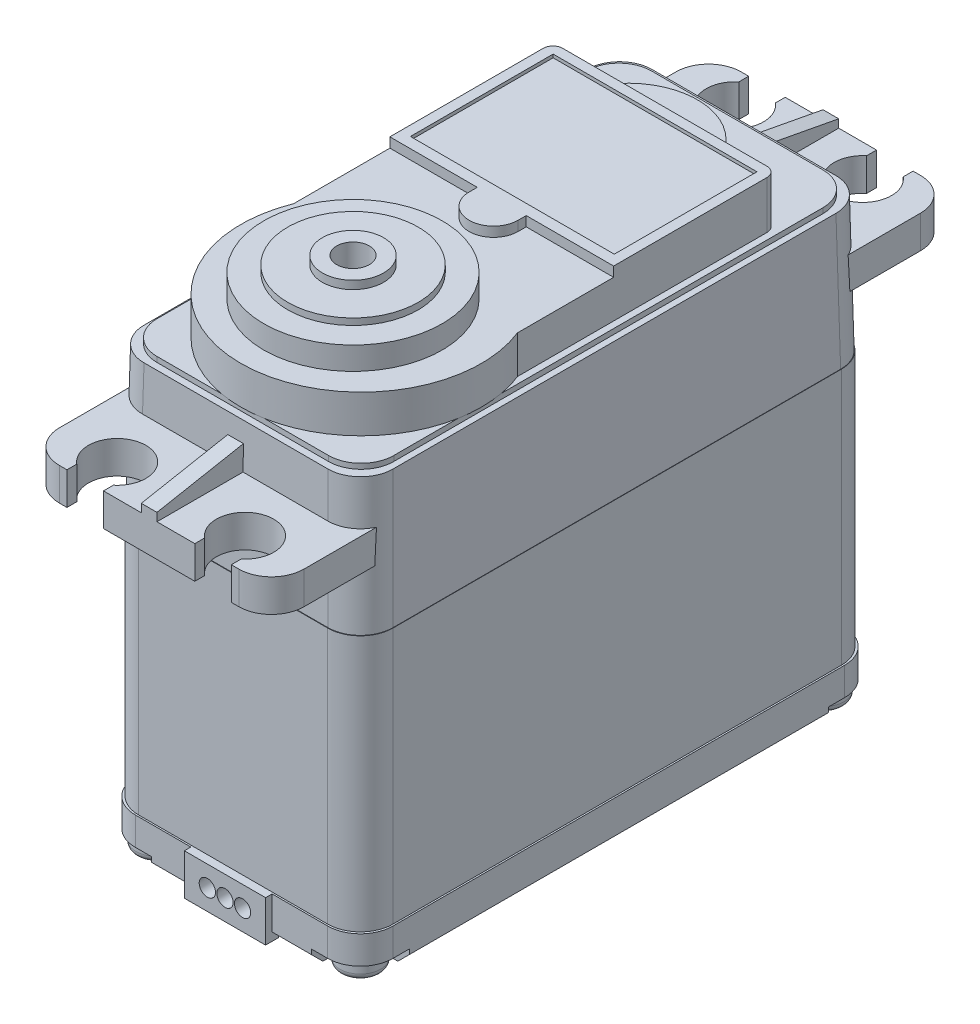
SolidWorks part; units mm, degrees
material "ABS"
ref_plane "Front Plane" through (0, 0, 0) normal (0, 0, 1) x (1, 0, 0)
ref_plane "Top Plane" through (0, 0, 0) normal (0, 1, 0) x (1, 0, 0)
ref_plane "Right Plane" through (0, 0, 0) normal (1, 0, 0) x (0, 0, -1)
sketch "Sketch1" plane through (0, 0, 0) normal (0, 1, 0) x (1, 0, 0)
  line L1 (-9.906, 20.0025) -> (9.906, 20.0025)
  line L2 (-9.906, 20.0025) -> (-9.906, -20.0025)
  line L3 (-9.906, -20.0025) -> (9.906, -20.0025)
  line L4 (9.906, 20.0025) -> (9.906, -20.0025)
  line L5 (-9.906, 20.0025) -> (9.906, -20.0025) construction
  line L6 (-9.906, -20.0025) -> (9.906, 20.0025) construction
  point P0 (0, 0)
  dimension "D1" = 19.812
  dimension "D2" = 40.005
extrude "Extrude1" add sketch "Sketch1" along normal blind 19.9644
sketch "Sketch2" plane through (0, 0, 0) normal (0, -1, 0) x (1, 0, 0)
  line L1 (-10.033, 20.1295) -> (10.033, 20.1295)
  line L2 (-10.033, 20.1295) -> (-10.033, -20.1295)
  line L3 (-10.033, -20.1295) -> (10.033, -20.1295)
  line L4 (10.033, 20.1295) -> (10.033, -20.1295)
  line L5 (-10.033, 20.1295) -> (10.033, -20.1295) construction
  line L6 (-10.033, -20.1295) -> (10.033, 20.1295) construction
  point P0 (0, 0)
  dimension "D1" = 40.259
  dimension "D2" = 20.066
extrude "Extrude2" add sketch "Sketch2" along normal blind 3.4544
sketch "Sketch3" plane through (0, 19.9644, 0) normal (0, 1, 0) x (1, 0, 0)
  line L1 (-9.8806, 19.9644) -> (9.8806, 19.9644)
  line L2 (-9.8806, 19.9644) -> (-9.8806, -19.9644)
  line L3 (-9.8806, -19.9644) -> (9.8806, -19.9644)
  line L4 (9.8806, 19.9644) -> (9.8806, -19.9644)
  line L5 (-9.8806, 19.9644) -> (9.8806, -19.9644) construction
  line L6 (-9.8806, -19.9644) -> (9.8806, 19.9644) construction
  point P0 (0, 0)
  dimension "D1" = 39.9288
  dimension "D2" = 19.7612
extrude "Extrude3" add sketch "Sketch3" along normal blind 10.5156 draft 1
sketch "Sketch4" plane through (0, 30.48, 0) normal (0, 1, 0) x (1, 0, 0)
  line L1 (-9.2202, 19.2532) -> (9.2202, 19.2532)
  line L2 (-9.2202, 19.2532) -> (-9.2202, -19.2532)
  line L3 (-9.2202, -19.2532) -> (9.2202, -19.2532)
  line L4 (9.2202, 19.2532) -> (9.2202, -19.2532)
  line L5 (-9.2202, 19.2532) -> (9.2202, -19.2532) construction
  line L6 (-9.2202, -19.2532) -> (9.2202, 19.2532) construction
  point P0 (0, 0)
  dimension "D1" = 18.4404
  dimension "D2" = 38.5064
extrude "Extrude4" add sketch "Sketch4" along normal blind 0.4064
fillet "Fillet1" radius 2.54 4 edges at (-9.2202, 30.6832, 19.2532) (9.2202, 30.6832, 19.2532) (9.2202, 30.6832, -19.2532) (-9.2202, 30.6832, -19.2532)
fillet "Fillet2" radius 2.54 4 edges at (-9.7888, 25.2222, 19.8726) (9.7888, 25.2222, 19.8726) (9.7888, 25.2222, -19.8726) (-9.7888, 25.2222, -19.8726)
fillet "Fillet3" radius 2.54 4 edges at (9.906, 9.9822, 20.0025) (-9.906, 9.9822, 20.0025) (-9.906, 9.9822, -20.0025) (9.906, 9.9822, -20.0025)
fillet "Fillet4" radius 2.54 4 edges at (10.033, -1.7272, -20.1295) (10.033, -1.7272, 20.1295) (-10.033, -1.7272, 20.1295) (-10.033, -1.7272, -20.1295)
sketch "Sketch5" plane through (0, -3.4544, 0) normal (0, -1, 0) x (1, 0, 0)
  line L0 (0, 20.1295) -> (0, -20.1295) construction
  line L1 (7.493, 20.1295) -> (-7.493, 20.1295) construction
  line L2 (-6.223, 20.1295) -> (6.223, 20.1295) construction
  line L3 (-6.223, -20.1295) -> (6.223, -20.1295) construction
  line L4 (10.033, 0) -> (-10.033, 0) construction
  line L5 (-10.033, 17.5895) -> (-10.033, -17.5895) construction
  line L6 (-10.033, 16.3195) -> (-10.033, -16.3195) construction
  line L7 (10.033, 16.3195) -> (10.033, -16.3195) construction
  line L8 (-6.223, 20.1295) -> (-6.223, 16.3195)
  line L9 (6.223, 20.1295) -> (6.223, 16.3195)
  line L10 (-10.033, 16.3195) -> (-6.223, 16.3195)
  line L11 (10.033, 16.3195) -> (6.223, 16.3195)
  line L12 (-10.033, -16.3195) -> (-6.223, -16.3195)
  line L13 (-6.223, -20.1295) -> (-6.223, -16.3195)
  line L14 (6.223, -20.1295) -> (6.223, -16.3195)
  line L15 (10.033, -16.3195) -> (6.223, -16.3195)
  line L16 (-7.493, 20.1295) -> (-6.223, 20.1295)
  line L17 (-10.033, 17.5895) -> (-10.033, 16.3195)
  line L18 (6.223, 20.1295) -> (7.493, 20.1295)
  line L19 (10.033, 17.5895) -> (10.033, 16.3195)
  line L20 (-10.033, -17.5895) -> (-10.033, -16.3195)
  line L21 (-7.493, -20.1295) -> (-6.223, -20.1295)
  line L22 (6.223, -20.1295) -> (7.493, -20.1295)
  line L23 (10.033, -16.3195) -> (10.033, -17.5895)
  arc A0 (-10.033, -17.5895) -> (-7.493, -20.1295) centre (-7.493, -17.5895) ccw construction
  arc A1 (-7.493, 20.1295) -> (-10.033, 17.5895) centre (-7.493, 17.5895) ccw construction
  arc A2 (10.033, 17.5895) -> (7.493, 20.1295) centre (7.493, 17.5895) ccw construction
  arc A3 (7.493, -20.1295) -> (10.033, -17.5895) centre (7.493, -17.5895) ccw construction
  arc A4 (-10.033, -17.5895) -> (-7.493, -20.1295) centre (-7.493, -17.5895) ccw
  arc A5 (7.493, -20.1295) -> (10.033, -17.5895) centre (7.493, -17.5895) ccw
  arc A6 (10.033, 17.5895) -> (7.493, 20.1295) centre (7.493, 17.5895) ccw
  arc A7 (-7.493, 20.1295) -> (-10.033, 17.5895) centre (-7.493, 17.5895) ccw
  dimension "D1" = 3.81
  dimension "D2" = 3.81
extrude "Extrude5" cut sketch "Sketch5" against normal blind 1.27
sketch "Sketch6" plane through (0, -2.1844, 0) normal (0, -1, 0) x (1, 0, 0)
  line L0 (0, 18.034) -> (0, -18.034) construction
  line L1 (-7.9375, 18.034) -> (7.9375, 18.034) construction
  line L2 (-7.9375, -18.034) -> (7.9375, -18.034) construction
  circle A0 centre (-7.9375, 18.034) radius 1.5875
  circle A1 centre (7.9375, 18.034) radius 1.5875
  circle A2 centre (7.9375, -18.034) radius 1.5875
  circle A3 centre (-7.9375, -18.034) radius 1.5875
  dimension "D3" = 3.175
  dimension "D1" = 15.875
  dimension "D2" = 36.068
extrude "Extrude7" add sketch "Sketch6" along normal blind 1.27
fillet "Fillet5" radius 0.508 4 edges at (7.9375, -3.4544, -19.6215) (-7.9375, -3.4544, -19.6215) (7.9375, -3.4544, 16.4465) (-7.9375, -3.4544, 16.4465)
sketch "Sketch7" plane through (0, -3.4544, 0) normal (0, -1, 0) x (1, 0, 0)
  line L0 (-9.525, 18.034) -> (-6.35, 18.034) construction
  line L1 (6.35, 18.034) -> (9.525, 18.034) construction
  line L2 (-9.525, -18.034) -> (-6.35, -18.034) construction
  line L3 (6.35, -18.034) -> (9.525, -18.034) construction
  line L5 (-8.1187, -16.9698) -> (-7.7563, -16.9698)
  line L6 (-8.1187, -16.9698) -> (-8.1187, -19.0982)
  line L7 (-8.1187, -19.0982) -> (-7.7563, -19.0982)
  line L8 (-7.7563, -16.9698) -> (-7.7563, -19.0982)
  line L9 (-8.1187, -16.9698) -> (-7.7563, -19.0982) construction
  line L10 (-8.1187, -19.0982) -> (-7.7563, -16.9698) construction
  line L11 (7.7563, -16.9698) -> (8.1187, -16.9698)
  line L12 (7.7563, -16.9698) -> (7.7563, -19.0982)
  line L13 (7.7563, -19.0982) -> (8.1187, -19.0982)
  line L14 (8.1187, -16.9698) -> (8.1187, -19.0982)
  line L15 (7.7563, -16.9698) -> (8.1187, -19.0982) construction
  line L16 (7.7563, -19.0982) -> (8.1187, -16.9698) construction
  line L17 (-8.1187, 19.0982) -> (-7.7563, 19.0982)
  line L18 (-8.1187, 19.0982) -> (-8.1187, 16.9698)
  line L19 (-8.1187, 16.9698) -> (-7.7563, 16.9698)
  line L20 (-7.7563, 19.0982) -> (-7.7563, 16.9698)
  line L21 (-8.1187, 19.0982) -> (-7.7563, 16.9698) construction
  line L22 (-8.1187, 16.9698) -> (-7.7563, 19.0982) construction
  line L23 (7.7563, 19.0982) -> (8.1187, 19.0982)
  line L24 (7.7563, 19.0982) -> (7.7563, 16.9698)
  line L25 (7.7563, 16.9698) -> (8.1187, 16.9698)
  line L26 (8.1187, 19.0982) -> (8.1187, 16.9698)
  line L27 (7.7563, 19.0982) -> (8.1187, 16.9698) construction
  line L28 (7.7563, 16.9698) -> (8.1187, 19.0982) construction
  circle A0 centre (-7.9375, 18.034) radius 1.5875 construction
  circle A1 centre (7.9375, 18.034) radius 1.5875 construction
  circle A2 centre (-7.9375, -18.034) radius 1.5875 construction
  circle A3 centre (-7.9375, -18.034) radius 1.5875 construction
  circle A4 centre (7.9375, -18.034) radius 1.5875 construction
  circle A5 centre (-7.9375, -18.034) radius 1.0795 construction
  circle A6 centre (7.9375, -18.034) radius 1.0795 construction
  circle A7 centre (-7.9375, 18.034) radius 1.0795 construction
  circle A8 centre (7.9375, 18.034) radius 1.0795 construction
  point P20 (-7.9375, -18.034)
  point P27 (7.9375, -18.034)
  point P34 (-7.9375, 18.034)
  point P41 (7.9375, 18.034)
extrude "Extrude8" cut sketch "Sketch7" against normal blind 0.508
sketch "Sketch8" plane through (0, -3.4544, 0) normal (0, -1, 0) x (1, 0, 0)
  line L0 (-7.9375, 19.6215) -> (-7.9375, 16.4465) construction
  line L1 (7.9375, 19.6215) -> (7.9375, 16.4465) construction
  line L2 (-7.9375, -16.4465) -> (-7.9375, -19.6215) construction
  line L3 (7.9375, -16.4465) -> (7.9375, -19.6215) construction
  line L4 (-7.7563, 19.0982) -> (-8.1187, 19.0982) construction
  line L5 (-9.0017, 18.2152) -> (-6.8733, 18.2152)
  line L6 (-9.0017, 18.2152) -> (-9.0017, 17.8528)
  line L7 (-9.0017, 17.8528) -> (-6.8733, 17.8528)
  line L8 (-6.8733, 18.2152) -> (-6.8733, 17.8528)
  line L9 (-9.0017, 18.2152) -> (-6.8733, 17.8528) construction
  line L10 (-9.0017, 17.8528) -> (-6.8733, 18.2152) construction
  line L12 (9.0017, 18.2152) -> (6.8733, 18.2152)
  line L13 (9.0017, 18.2152) -> (9.0017, 17.8528)
  line L14 (9.0017, 17.8528) -> (6.8733, 17.8528)
  line L15 (6.8733, 18.2152) -> (6.8733, 17.8528)
  line L16 (9.0017, 18.2152) -> (6.8733, 17.8528) construction
  line L17 (9.0017, 17.8528) -> (6.8733, 18.2152) construction
  line L18 (-9.0017, -17.8528) -> (-6.8733, -17.8528)
  line L19 (-9.0017, -17.8528) -> (-9.0017, -18.2152)
  line L20 (-9.0017, -18.2152) -> (-6.8733, -18.2152)
  line L21 (-6.8733, -17.8528) -> (-6.8733, -18.2152)
  line L22 (-9.0017, -17.8528) -> (-6.8733, -18.2152) construction
  line L23 (-9.0017, -18.2152) -> (-6.8733, -17.8528) construction
  line L24 (6.8733, -17.8528) -> (9.0017, -17.8528)
  line L25 (6.8733, -17.8528) -> (6.8733, -18.2152)
  line L26 (6.8733, -18.2152) -> (9.0017, -18.2152)
  line L27 (9.0017, -17.8528) -> (9.0017, -18.2152)
  line L28 (6.8733, -17.8528) -> (9.0017, -18.2152) construction
  line L29 (6.8733, -18.2152) -> (9.0017, -17.8528) construction
  circle A0 centre (-7.9375, 18.034) radius 1.5875 construction
  circle A1 centre (7.9375, 18.034) radius 1.5875 construction
  circle A2 centre (7.9375, 18.034) radius 1.5875 construction
  circle A3 centre (-7.9375, -18.034) radius 1.5875 construction
  circle A4 centre (7.9375, -18.034) radius 1.5875 construction
  arc A5 (-7.7563, 16.9698) -> (-7.7563, 19.0982) centre (-7.9375, 18.034) ccw construction
  arc A6 (7.7563, 19.0982) -> (7.7563, 16.9698) centre (7.9375, 18.034) ccw construction
  arc A7 (-7.7563, -19.0982) -> (-7.7563, -16.9698) centre (-7.9375, -18.034) ccw construction
  arc A8 (8.1187, -19.0982) -> (8.1187, -16.9698) centre (7.9375, -18.034) ccw construction
  point P21 (-7.9375, 18.034)
  point P31 (7.9375, 18.034)
  point P39 (-7.9375, -18.034)
  point P47 (7.9375, -18.034)
extrude "Extrude9" cut sketch "Sketch8" against normal blind 0.508
ref_plane "Plane1" through (0, 27.0256, 0) normal (0, -1, 0) x (1, 0, 0)
sketch "Sketch9" plane through (0, 27.0256, 0) normal (0, -1, 0) x (1, 0, 0)
  line L0 (0, -26.543) -> (0, 26.543) construction
  line L1 (-9.525, -26.543) -> (9.525, -26.543)
  line L2 (-9.525, 26.543) -> (9.525, 26.543)
  line L3 (-9.525, -26.543) -> (-9.525, 26.543)
  line L4 (9.525, -26.543) -> (9.525, 26.543)
  dimension "D1" = 53.086
  dimension "D2" = 19.05
extrude "Extrude10" add sketch "Sketch9" along normal blind 2.54
sketch "Sketch10" plane through (0, 27.0256, 0) normal (0, 1, 0) x (1, 0, 0)
  line L0 (0, 24.0538) -> (0, -24.0538) construction
  line L1 (4.9784, 24.0538) -> (-4.9784, 24.0538) construction
  line L2 (4.9784, -24.0538) -> (-4.9784, -24.0538) construction
  circle A0 centre (4.9784, 24.0538) radius 2.2352
  circle A1 centre (-4.9784, 24.0538) radius 2.2352
  circle A2 centre (4.9784, -24.0538) radius 2.2352
  circle A3 centre (-4.9784, -24.0538) radius 2.2352
  dimension "D3" = 4.4704
  dimension "D1" = 48.1076
  dimension "D2" = 9.9568
extrude "Extrude11" cut sketch "Sketch10" against normal through all
sketch "Sketch11" plane through (0, 27.0256, 0) normal (0, 1, 0) x (1, 0, 0)
  line L0 (-7.2136, 24.0538) -> (-2.7432, 24.0538) construction
  line L1 (2.7432, 24.0538) -> (7.2136, 24.0538) construction
  line L2 (-7.2136, -24.0538) -> (-2.7432, -24.0538) construction
  line L3 (2.7432, -24.0538) -> (7.2136, -24.0538) construction
  line L5 (-6.4008, 24.0538) -> (-3.556, 24.0538)
  line L6 (-6.4008, 24.0538) -> (-6.4008, 30.4038)
  line L7 (-6.4008, 30.4038) -> (-3.556, 30.4038)
  line L8 (-3.556, 24.0538) -> (-3.556, 30.4038)
  line L9 (3.556, 24.0538) -> (6.4008, 24.0538)
  line L10 (3.556, 24.0538) -> (3.556, 30.4038)
  line L11 (3.556, 30.4038) -> (6.4008, 30.4038)
  line L12 (6.4008, 24.0538) -> (6.4008, 30.4038)
  line L13 (-6.4008, -24.0538) -> (-3.556, -24.0538)
  line L14 (-6.4008, -24.0538) -> (-6.4008, -30.4038)
  line L15 (-6.4008, -30.4038) -> (-3.556, -30.4038)
  line L16 (-3.556, -24.0538) -> (-3.556, -30.4038)
  line L17 (3.556, -24.0538) -> (6.4008, -24.0538)
  line L18 (3.556, -24.0538) -> (3.556, -30.4038)
  line L19 (3.556, -30.4038) -> (6.4008, -30.4038)
  line L20 (6.4008, -24.0538) -> (6.4008, -30.4038)
  circle A0 centre (-4.9784, 24.0538) radius 2.2352 construction
  circle A1 centre (4.9784, 24.0538) radius 2.2352 construction
  circle A2 centre (-4.9784, -24.0538) radius 2.2352 construction
  circle A3 centre (4.9784, -24.0538) radius 2.2352 construction
  point P27 (-4.9784, 24.0538)
  point P28 (4.9784, 24.0538)
  point P29 (-4.9784, -24.0538)
  point P30 (4.9784, -24.0538)
  dimension "D1" = 2.8448
  dimension "D2" = 6.35
extrude "Extrude12" cut sketch "Sketch11" against normal through all
fillet "Fillet6" radius 2.54 4 edges at (9.525, 25.7556, 26.543) (-9.525, 25.7556, 26.543) (9.525, 25.7556, -26.543) (-9.525, 25.7556, -26.543)
sketch "Sketch12" plane through (0, -3.4544, 0) normal (0, -1, 0) x (1, 0, 0)
  circle A0 centre (0, 0) radius 0.9525
  dimension "D1" = 1.905
extrude "Extrude13" cut sketch "Sketch12" against normal blind 0.635
fillet "Fillet7" radius 0.254 1 edges at (0, -2.8194, -0.9525)
chamfer "Chamfer1" distance 0.889 angle 45 4 edges at (10.033, -3.4544, 0) (0, -3.4544, 20.1295) (0, -3.4544, -20.1295) (-10.033, -3.4544, 0)
sketch "Sketch13" plane through (0, 30.8864, 0) normal (0, 1, 0) x (1, 0, 0)
  line L0 (0, -19.7808) -> (0, -19.4056) construction
  line L1 (-6.6802, -19.2532) -> (6.6802, -19.2532) construction
  line L2 (-8.7122, 13.6144) -> (-4.572, 13.6144)
  line L3 (-7.1574, -19.7808) -> (7.1574, -19.7808) construction
  line L4 (0, -19.4056) -> (0, -19.2532) construction
  line L5 (0, -19.2532) -> (0, 13.6144) construction
  line L6 (-8.7122, 13.6144) -> (-8.7122, -6.5771)
  line L7 (8.7122, 13.6144) -> (8.7122, -6.5771)
  line L8 (0, 13.6144) -> (0, 16.1544) construction
  line L9 (-4.572, 13.6144) -> (4.572, 13.6144) construction
  line L10 (4.572, 13.6144) -> (8.7122, 13.6144)
  arc A0 (-8.7122, -6.5771) -> (8.7122, -6.5771) centre (0, -10.033) ccw
  arc A1 (-4.572, 13.6144) -> (4.572, 13.6144) centre (0, 10.7696) cw
  dimension "D1" = 18.7452
  dimension "D2" = 0.1524
  dimension "D3" = 17.4244
  dimension "D4" = 33.02
  dimension "D5" = 9.144
  dimension "D6" = 4.572
  dimension "D7" = 2.54
extrude "Extrude14" add sketch "Sketch13" along normal blind 2.9464
sketch "Sketch14" plane through (0, 33.8328, 0) normal (0, 1, 0) x (1, 0, 0)
  line L0 (8.7122, -6.5771) -> (8.7122, 13.6144) construction
  line L1 (-8.7122, 13.6144) -> (8.7122, 13.6144)
  line L2 (-8.7122, 13.6144) -> (-8.7122, 0.9144)
  line L3 (-8.7122, 0.9144) -> (-1.905, 0.9144)
  line L4 (8.7122, 13.6144) -> (8.7122, 0.9144)
  line L5 (0, 0.9144) -> (0, 13.6144) construction
  line L6 (0, 0.9144) -> (0, 0.2794) construction
  line L7 (0, 0.2794) -> (0, -1.6256) construction
  line L8 (-1.905, 0.2794) -> (-1.905, 0.9144)
  line L9 (1.905, 0.2794) -> (1.905, 0.9144)
  line L10 (1.905, 0.9144) -> (8.7122, 0.9144)
  arc A0 (-1.905, 0.2794) -> (1.905, 0.2794) centre (0, 0.2794) ccw
  dimension "D2" = 0.635
  dimension "D3" = 3.81
  dimension "D1" = 12.7
extrude "Extrude15" add sketch "Sketch14" along normal blind 0.762
sketch "Sketch15" plane through (0, 34.5948, 0) normal (0, 1, 0) x (1, 0, 0)
  line L0 (0, 13.6144) -> (0, 12.8524) construction
  line L1 (-7.9375, 12.8524) -> (7.9375, 12.8524)
  line L2 (-7.9375, 12.8524) -> (-7.9375, 1.7399)
  line L3 (-7.9375, 1.7399) -> (7.9375, 1.7399)
  line L4 (7.9375, 12.8524) -> (7.9375, 1.7399)
  line L5 (8.7122, 13.6144) -> (-8.7122, 13.6144) construction
  dimension "D1" = 15.875
  dimension "D2" = 11.1125
  dimension "D3" = 0.762
extrude "Extrude16" cut sketch "Sketch15" against normal blind 0.254
fillet "Fillet8" radius 0.762 2 edges at (-8.7122, 32.7406, -13.6144) (8.7122, 32.7406, -13.6144)
sketch "Sketch16" plane through (0, 33.8328, 0) normal (0, 1, 0) x (1, 0, 0)
  line L0 (0, -26.543) -> (0, -10.668) construction
  line L1 (3.556, -26.543) -> (-3.556, -26.543) construction
  circle A0 centre (0, -10.668) radius 6.9469
  dimension "D2" = 13.8938
  dimension "D1" = 15.875
extrude "Extrude17" add sketch "Sketch16" along normal blind 1.778
sketch "Sketch17" plane through (0, 35.6108, 0) normal (0, 1, 0) x (1, 0, 0)
  circle A0 centre (0, -10.668) radius 5.08
  dimension "D1" = 10.16
extrude "Extrude18" add sketch "Sketch17" along normal blind 0.508
sketch "Sketch18" plane through (0, 36.1188, 0) normal (0, 1, 0) x (1, 0, 0)
  circle A0 centre (0, -10.668) radius 2.3813
  dimension "D1" = 4.7625
extrude "Extrude19" add sketch "Sketch18" along normal blind 0.635
sketch "Sketch19" plane through (0, 36.7538, 0) normal (0, 1, 0) x (1, 0, 0)
  circle A0 centre (0, -10.668) radius 1.27
  dimension "D1" = 2.54
extrude "Extrude20" cut sketch "Sketch19" against normal blind 3.175
sketch "Sketch20" plane through (0, 0, 20.1295) normal (0, 0, 1) x (1, 0, 0)
  line L1 (-3.1623, 0) -> (3.1623, 0)
  line L2 (-3.1623, 0) -> (-3.1623, -3.2004)
  line L3 (-3.1623, -3.2004) -> (3.1623, -3.2004)
  line L4 (3.1623, 0) -> (3.1623, -3.2004)
  dimension "D1" = 6.3246
  dimension "D2" = 3.2004
extrude "Extrude21" add sketch "Sketch20" along normal blind 0.508 and the other way blind 0.508
sketch "Sketch21" plane through (0, 0, 20.6375) normal (0, 0, 1) x (1, 0, 0)
  line L0 (0, 0) -> (0, -3.2004) construction
  line L1 (-3.1623, -3.2004) -> (3.1623, -3.2004) construction
  line L2 (0, -1.6002) -> (1.3716, -1.6002) construction
  line L3 (0, -1.6002) -> (-1.3716, -1.6002) construction
  circle A0 centre (0, -1.6002) radius 0.635
  circle A1 centre (1.3716, -1.6002) radius 0.635
  circle A2 centre (-1.3716, -1.6002) radius 0.635
  dimension "D1" = 1.27
  dimension "D2" = 2.7432
extrude "Extrude22" cut sketch "Sketch21" against normal blind 2.54
sketch "Sketch22" plane through (0, 0, 0) normal (1, 0, 0) x (0, 0, -1)
  line L0 (-19.8079, 28.9306) -> (-26.543, 27.6606)
  line L1 (-19.8411, 27.0256) -> (-19.7808, 30.48) construction
  line L2 (-26.543, 27.6606) -> (-26.543, 27.0256)
  line L3 (-26.543, 27.0256) -> (-19.8411, 27.0256)
  line L4 (-19.8411, 27.0256) -> (-19.8079, 28.9306)
  line L5 (19.8411, 27.0256) -> (26.543, 27.0256)
  line L6 (26.543, 27.0256) -> (26.543, 27.6606)
  line L7 (26.543, 27.6606) -> (19.8079, 28.9306)
  line L8 (19.7808, 30.48) -> (19.8411, 27.0256) construction
  line L9 (19.8079, 28.9306) -> (19.8411, 27.0256)
  dimension "D1" = 3.175
  dimension "D2" = 4.445
extrude "Extrude23" add sketch "Sketch22" along normal mid plane 1.2192
